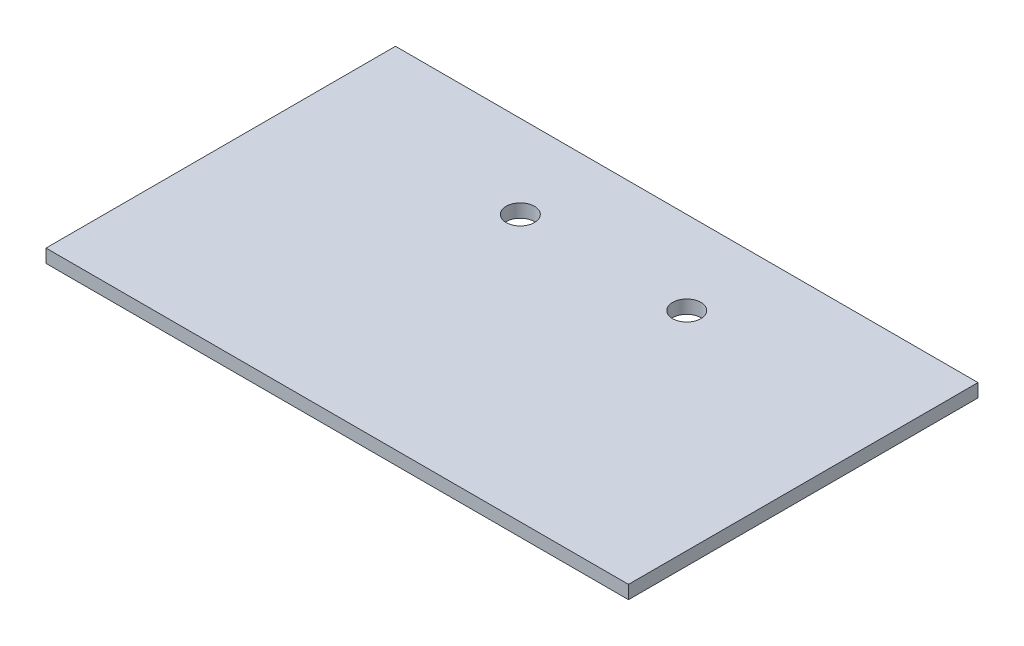
SolidWorks part; units mm, degrees
ref_plane "Front Plane" through (0, 0, 0) normal (0, 0, 1) x (1, 0, 0)
ref_plane "Top Plane" through (0, 0, 0) normal (0, 1, 0) x (1, 0, 0)
ref_plane "Right Plane" through (0, 0, 0) normal (1, 0, 0) x (0, 0, -1)
sketch "Sketch1" plane through (0, 0, 0) normal (0, 1, 0) x (1, 0, 0)
  line L1 (-35, -21) -> (35, -21)
  line L2 (-35, -21) -> (-35, 21)
  line L3 (-35, 21) -> (35, 21)
  line L4 (35, -21) -> (35, 21)
  line L5 (-35, -21) -> (35, 21) construction
  line L6 (-35, 21) -> (35, -21) construction
  point P0 (0, 0)
  dimension "D1" = 70
  dimension "D2" = 42
extrude "Boss-Extrude1" add sketch "Sketch1" along normal blind 1.6
hole_wizard "M3 Clearance Hole1" positions "Sketch3" profile "Sketch4" hole size "M3" standard "DIN"
sketch "Sketch3" plane through (0, 1.6, 0) normal (0, 1, 0) x (1, 0, 0)
  line L0 (0, 21) -> (0, -21) construction
  line L1 (35, 21) -> (-35, 21) construction
  line L2 (-35, -21) -> (35, -21) construction
  point P0 (-10, 11)
  dimension "D1" = 20
  dimension "D2" = 10
sketch "Sketch4" plane through (-10, 1.6, -11) normal (1, 0, 0) x (0, 0, 1)
  line L0 (0, 0) -> (0, 2.6205)
  line L1 (0, 2.6205) -> (1.7, 1.599)
  line L2 (1.7, 1.599) -> (1.7, 0)
  line L5 (1.7, 0) -> (0, 0)
  line L10 (0, 2.6205) -> (-1.7, 1.599) construction
  line L11 (0, -6.35) -> (0, 107.95) construction
  dimension "Hole Dia." = 3.4
  dimension "Hole Depth" = 1.599
  dimension "Drill Angle" = 118
mirror "Mirror1" about plane through (0, 0, 0) normal (1, 0, 0) of "M3 Clearance Hole1"
